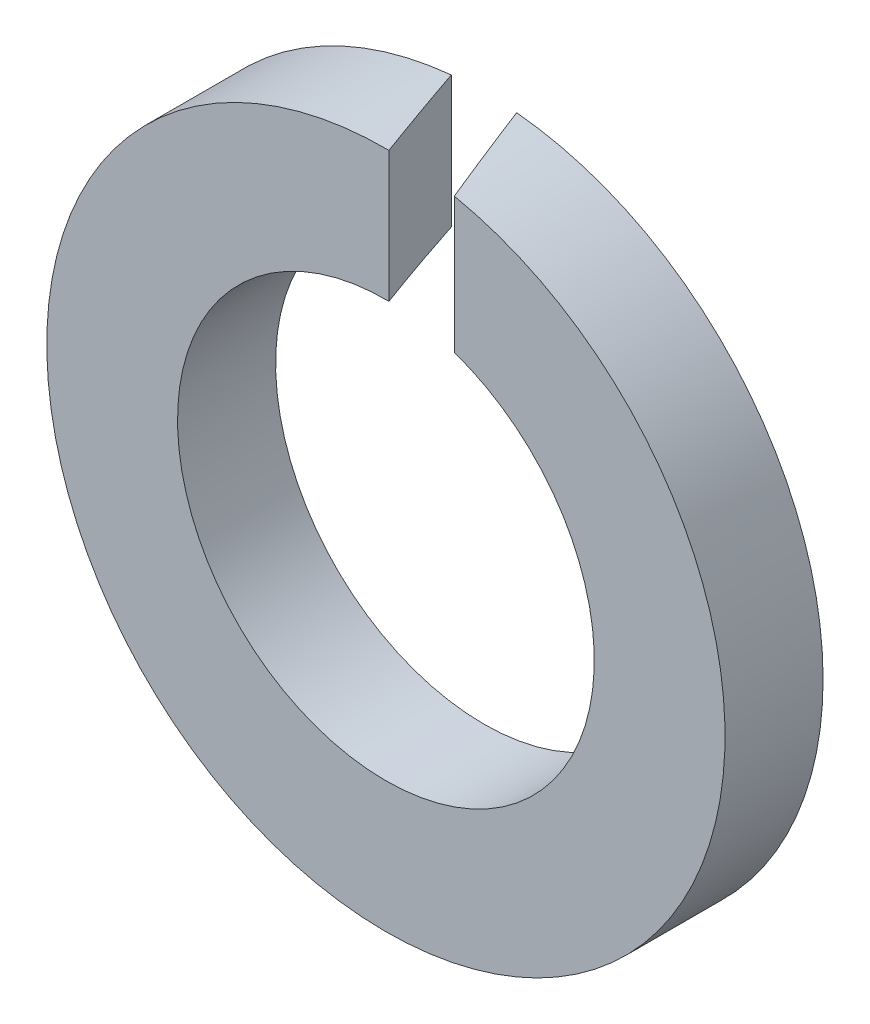
SolidWorks part; units mm, degrees
ref_plane "Plane1" through (0, 0, 0) normal (0, 0, 1) x (1, 0, 0)
ref_plane "Plane2" through (0, 0, 0) normal (0, 1, 0) x (1, 0, 0)
ref_plane "Plane3" through (0, 0, 0) normal (1, 0, 0) x (0, 0, -1)
sketch "Эскиз1" plane through (0, 0, 0) normal (0, 0, 1) x (1, 0, 0)
  circle A0 centre (0, 0) radius 2.55
  circle A1 centre (0, 0) radius 4.15
  dimension "D1" = 5.1
  dimension "D2" = 8.3
extrude "Вытянуть1" add sketch "Эскиз1" along normal blind 1.2
sketch "Эскиз2" plane through (0, 0, 0) normal (0, 1, 0) x (1, 0, 0)
  line L0 (-0.652, 0.6924) -> (0.1431, 0.7057)
  line L1 (0.7722, -3.2207) -> (1.4838, -2.9778)
  line L6 (1.4838, -2.9778) -> (0.1431, 0.7057)
  line L7 (0.7722, -3.2207) -> (-0.652, 0.6924)
extrude "Вырез-Вытянуть3" cut sketch "Эскиз2" along normal through all
